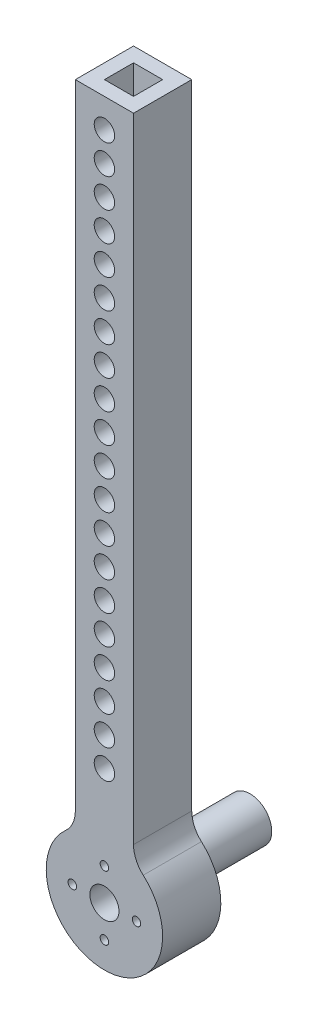
SolidWorks part; units mm, degrees
ref_plane "Front Plane" through (0, 0, 0) normal (0, 0, 1) x (1, 0, 0)
ref_plane "Top Plane" through (0, 0, 0) normal (0, 1, 0) x (1, 0, 0)
ref_plane "Right Plane" through (0, 0, 0) normal (1, 0, 0) x (0, 0, -1)
sketch "Sketch1" plane through (0, 0, 0) normal (0, 1, 0) x (1, 0, 0)
  line L0 (-3.175, -3.175) -> (-3.175, 3.175)
  line L1 (-6.35, -6.35) -> (6.35, -6.35)
  line L2 (-6.35, -6.35) -> (-6.35, 6.35)
  line L3 (-6.35, 6.35) -> (6.35, 6.35)
  line L4 (6.35, -6.35) -> (6.35, 6.35)
  line L5 (-6.35, -6.35) -> (6.35, 6.35) construction
  line L6 (-6.35, 6.35) -> (6.35, -6.35) construction
  line L7 (-3.175, 3.175) -> (3.175, 3.175)
  line L8 (3.175, -3.175) -> (3.175, 3.175)
  line L9 (-3.175, -3.175) -> (3.175, -3.175)
  point P0 (0, 0)
  dimension "D1" = 12.7
  dimension "D2" = 3.175
extrude "Boss-Extrude1" add sketch "Sketch1" along normal blind 152.4
sketch "Sketch2" plane through (0, 0, 6.35) normal (0, 0, 1) x (1, 0, 0)
  line L0 (-6.35, 0) -> (6.35, 0) construction
  circle A0 centre (0, 25.4) radius 2.227
  circle A10 centre (0, 31.75) radius 2.227
  circle A11 centre (0, 38.1) radius 2.227
  circle A12 centre (0, 44.45) radius 2.227
  circle A13 centre (0, 50.8) radius 2.227
  circle A14 centre (0, 57.15) radius 2.227
  circle A15 centre (0, 63.5) radius 2.227
  circle A16 centre (0, 69.85) radius 2.227
  circle A17 centre (0, 76.2) radius 2.227
  circle A18 centre (0, 82.55) radius 2.227
  circle A19 centre (0, 88.9) radius 2.227
  circle A20 centre (0, 95.25) radius 2.227
  circle A21 centre (0, 101.6) radius 2.227
  circle A22 centre (0, 107.95) radius 2.227
  circle A23 centre (0, 114.3) radius 2.227
  circle A24 centre (0, 120.65) radius 2.227
  circle A25 centre (0, 127) radius 2.227
  circle A26 centre (0, 133.35) radius 2.227
  circle A27 centre (0, 139.7) radius 2.227
  circle A28 centre (0, 146.05) radius 2.227
  dimension "D2" = 4.454
  dimension "D1" = 25.4
  dimension "D3" = 20
extrude "Cut-Extrude1" cut sketch "Sketch2" against normal through all
sketch "Sketch3" plane through (0, 0, 6.35) normal (0, 0, 1) x (1, 0, 0)
  circle A0 centre (0, 0) radius 12.7
  dimension "D1" = 25.4
extrude "Boss-Extrude2" add sketch "Sketch3" against normal blind 12.7
sketch "Sketch4" plane through (0, 0, 6.35) normal (0, 0, 1) x (1, 0, 0)
  circle A0 centre (0, 0) radius 4.7625
  dimension "D1" = 9.525
extrude "Boss-Extrude3" add sketch "Sketch4" against normal blind 31.75
sketch "Sketch6" plane through (0, 0, 6.35) normal (0, 0, 1) x (1, 0, 0)
  circle A0 centre (0, 0) radius 3.175
  circle A1 centre (7, 0) radius 0.927
  circle A2 centre (0, -7) radius 0.927
  circle A3 centre (-7, 0) radius 0.927
  circle A4 centre (0, 7) radius 0.927
  point P14 (0, 0)
  dimension "D1" = 6.35
  dimension "D2" = 1.854
  dimension "D3" = 7
  dimension "D4" = 4
extrude "Cut-Extrude3" cut sketch "Sketch6" against normal through all
fillet "Fillet2" radius 6.35 2 edges at (-6.35, 10.9985, 0) (6.35, 10.9985, 0)
equation "\"tighttol\" = 0.005in"
equation "\"normtol\" = 0.01in"
equation "\"loosetol\" = 0.02in"
equation "\"Fry height\"= 0.5in"
equation "\"Fry spacing\"= 0.5625in"
equation "\"Potato width\"= \"Fry spacing\" * 4"
equation "\"Potato length\"= 80mm"
equation "\"D2@Sketch6\"=1.6mm+\"normtol\""
equation "\"D3@Sketch6\"=7mm"
